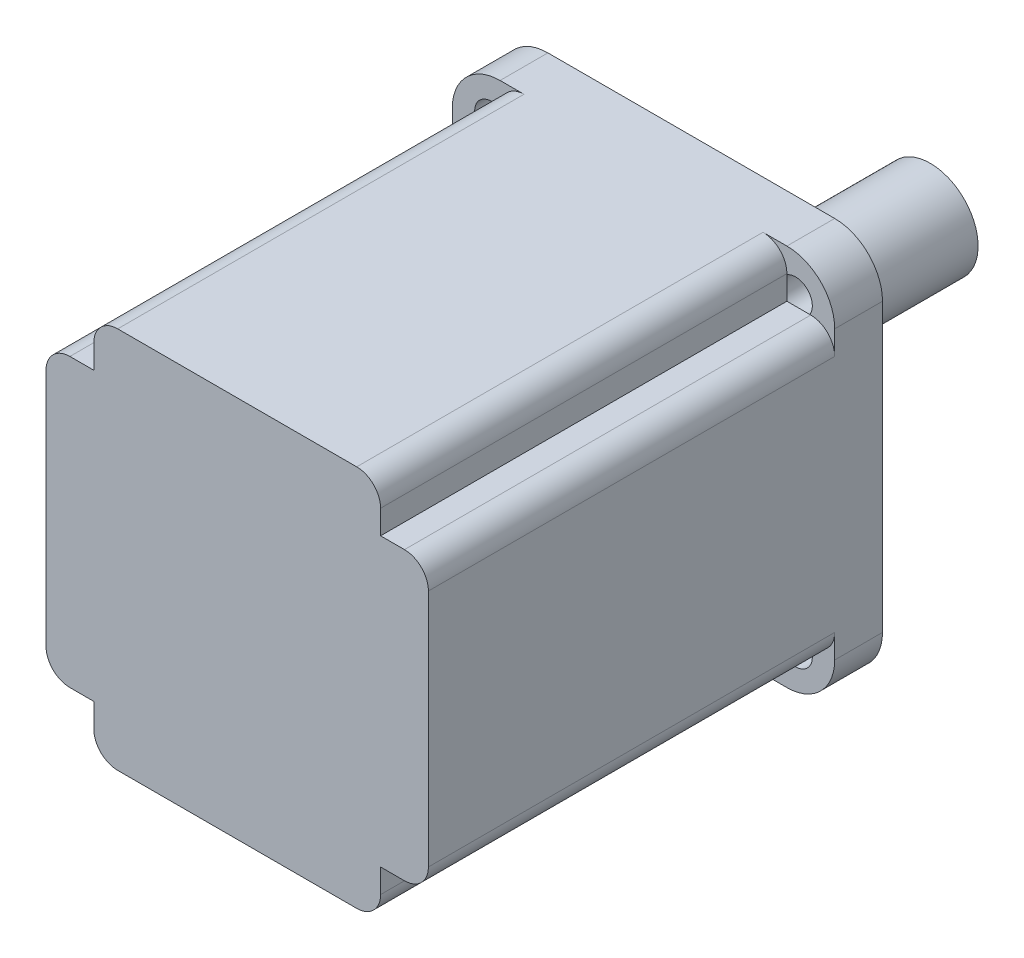
SolidWorks part; units mm, degrees
ref_plane "前视基准面" through (0, 0, 0) normal (0, 0, 1) x (1, 0, 0)
ref_plane "上视基准面" through (0, 0, 0) normal (0, 1, 0) x (1, 0, 0)
ref_plane "右视基准面" through (0, 0, 0) normal (1, 0, 0) x (0, 0, -1)
sketch "草图1" plane through (0, 0, 0) normal (0, 0, 1) x (1, 0, 0)
  line L0 (-136.3118, 0) -> (164.2586, 0) construction
  line L1 (-40, 40) -> (40, 40)
  line L2 (-40, 40) -> (-40, -40)
  line L3 (-40, -40) -> (40, -40)
  line L4 (40, 40) -> (40, -40)
  line L5 (-40, 40) -> (40, -40) construction
  line L6 (-40, -40) -> (40, 40) construction
  line L7 (0, 89.3541) -> (0, -97.1478) construction
  line L9 (-32.5, 32.5) -> (32.5, 32.5) construction
  line L10 (-32.5, 32.5) -> (-32.5, -32.5) construction
  line L11 (-32.5, -32.5) -> (32.5, -32.5) construction
  line L12 (32.5, 32.5) -> (32.5, -32.5) construction
  line L13 (-32.5, 32.5) -> (32.5, -32.5) construction
  line L14 (-32.5, -32.5) -> (32.5, 32.5) construction
  point P0 (0, 0)
  point P10 (0, 0)
  dimension "D3" = 65
  dimension "D1" = 80
  dimension "D2" = 80
extrude "凸台-拉伸1" add sketch "草图1" along normal blind 95
sketch "草图2" plane through (0, 0, 0) normal (0, 0, -1) x (-1, 0, 0)
  circle A0 centre (0, 0) radius 10
  dimension "D1" = 20
extrude "凸台-拉伸2" add sketch "草图2" along normal blind 50
sketch "草图3" plane through (0, 0, 95) normal (0, 0, 1) x (1, 0, 0)
  line L0 (-126.9071, 0) -> (137.1892, 0) construction
  line L1 (-40, 40) -> (-30, 40)
  line L2 (-40, 40) -> (-40, 30)
  line L3 (-40, 30) -> (-30, 30)
  line L4 (-30, 40) -> (-30, 30)
  line L5 (0, 116.4462) -> (0, -110.7211) construction
  line L6 (30, 40) -> (30, 30)
  line L7 (40, 30) -> (30, 30)
  line L8 (40, 40) -> (40, 30)
  line L9 (40, 40) -> (30, 40)
  line L10 (40, -40) -> (30, -40)
  line L11 (40, -40) -> (40, -30)
  line L12 (40, -30) -> (30, -30)
  line L13 (30, -40) -> (30, -30)
  line L14 (-30, -40) -> (-30, -30)
  line L15 (-40, -30) -> (-30, -30)
  line L16 (-40, -40) -> (-40, -30)
  line L17 (-40, -40) -> (-30, -40)
  dimension "D1" = 10
  dimension "D2" = 10
extrude "切除-拉伸1" cut sketch "草图3" against normal offset from surface (85 mm away) 10 up to face at (-10, 0, 0)
fillet "圆角1" radius 10 4 edges at (40, 40, 5) (40, -40, 5) (-40, 40, 5) (-40, -40, 5)
fillet "圆角3" radius 5 8 edges at (-40, -30, 52.5) (-30, -40, 52.5) (30, -40, 52.5) (40, -30, 52.5) (40, 30, 52.5) (30, 40, 52.5) (-40, 30, 52.5) (-30, 40, 52.5)
sketch "草图4" plane through (0, 0, 10) normal (0, 0, 1) x (1, 0, 0)
  circle A0 centre (0, 0) radius 45
  point P3 (31.8198, 31.8198)
  point P4 (-31.8198, 31.8198)
  point P5 (-31.8198, -31.8198)
  point P6 (31.8198, -31.8198)
  point P7 (0, 0)
  point P8 (51.369, 0)
  point P9 (43.2912, 12.6754)
  point P10 (44.1649, 48.5921)
  point P11 (31.8216, 31.818)
  point P12 (31.6283, 32.0101)
  dimension "D1" = 90
  dimension "D3" = 0
hole_wizard "大小mm 暗销槽口1" positions "3D草图1" profile "草图5" size "Ø6.0" standard "GB"
sketch3d "3D草图1"
  point P0 (-31.8198, 31.8198, 10)
  point P3 (31.8198, 31.8198, 10)
  point P6 (31.8198, -31.8198, 10)
  point P9 (-31.8198, -31.8198, 10)
sketch "草图5" plane through (-31.8198, 31.8198, 10) normal (1, 0, 0) x (0, -1, 0)
  line L0 (0, 0) -> (0, 62.103)
  line L1 (0, 62.103) -> (3.5, 60)
  line L2 (3.5, 60) -> (3.5, 0)
  line L5 (3.5, 0) -> (0, 0)
  line L10 (0, 62.103) -> (-3.5, 60) construction
  line L11 (0, -6.35) -> (0, 107.95) construction
  dimension "孔直径" = 7
  dimension "孔深度" = 60
  dimension "导头角度" = 118
